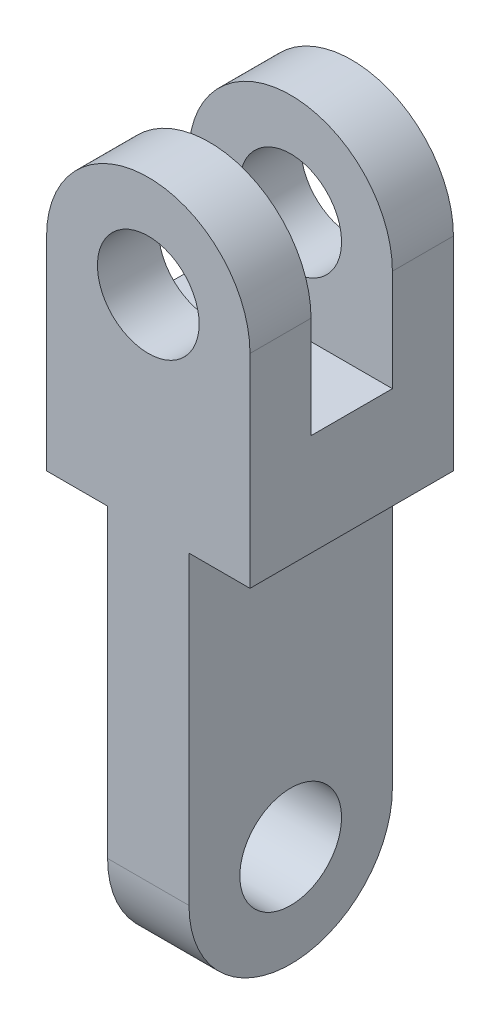
SolidWorks part; units mm, degrees
ref_plane "Alzado" through (0, 0, 0) normal (0, 0, 1) x (1, 0, 0)
ref_plane "Planta" through (0, 0, 0) normal (0, 1, 0) x (1, 0, 0)
ref_plane "Vista lateral" through (0, 0, 0) normal (1, 0, 0) x (0, 0, -1)
sketch "Croquis1" plane through (0, 0, 0) normal (0, 0, 1) x (1, 0, 0)
  line L0 (-50, 0) -> (50, 0)
  line L1 (50, 0) -> (50, 100)
  line L2 (-50, 100) -> (-50, 0)
  arc A0 (50, 100) -> (-50, 100) centre (0, 100) ccw
  circle A1 centre (0, 100) radius 25
  point P4 (0, 0)
  dimension "D1" = 50
  dimension "D2" = 50
  dimension "D3" = 100
extrude "Saliente-Extruir1" add sketch "Croquis1" along normal mid plane 100
sketch "Croquis2" plane through (50, 0, 0) normal (1, 0, 0) x (0, 0, -1)
  line L0 (-20, 150) -> (-20, 50)
  line L1 (50, 150) -> (-50, 150) construction
  line L2 (-20, 50) -> (20, 50)
  line L3 (20, 50) -> (20, 150)
  line L4 (20, 150) -> (-20, 150)
  point P4 (0, 50)
  dimension "D1" = 100
  dimension "D2" = 40
extrude "Cortar-Extruir1" cut sketch "Croquis2" against normal up to next
sketch "Croquis3" plane through (0, 0, 0) normal (1, 0, 0) x (0, 0, -1)
  line L0 (-50, 0) -> (-50, -150)
  line L1 (50, -150) -> (50, 0)
  line L2 (50, 0) -> (-50, 0)
  line L3 (-50, 0) -> (50, 0) construction
  line L4 (50, 0) -> (50, 100) construction
  line L5 (-50, 0) -> (-50, 100) construction
  arc A0 (-50, -150) -> (50, -150) centre (0, -150) ccw
  circle A1 centre (0, -150) radius 25
  dimension "D1" = 50
  dimension "D2" = 150
extrude "Saliente-Extruir2" add sketch "Croquis3" along normal mid plane 40
